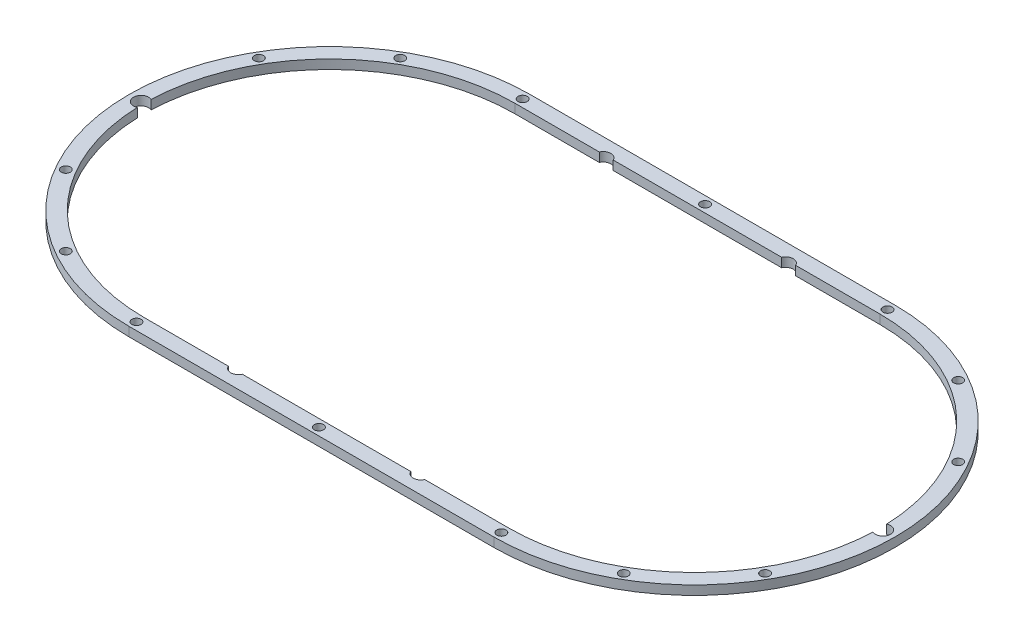
SolidWorks part; units mm, degrees
ref_plane "前视基准面" through (0, 0, 0) normal (0, 0, 1) x (1, 0, 0)
ref_plane "上视基准面" through (0, 0, 0) normal (0, 1, 0) x (1, 0, 0)
ref_plane "右视基准面" through (0, 0, 0) normal (1, 0, 0) x (0, 0, -1)
sketch "草图1" plane through (0, 0, 0) normal (0, 1, 0) x (1, 0, 0)
  line L0 (0, 0) -> (0, 89.0672) construction
  line L1 (-60, 0) -> (60, 0) construction
  line L2 (-60, 70) -> (60, 70)
  line L3 (-60, -70) -> (60, -70)
  line L4 (-90, 51.9615) -> (-60, 0) construction
  line L5 (-90, -51.9615) -> (-60, 0) construction
  line L8 (0, 0) -> (76.6344, 0) construction
  line L9 (-49.5811, 59.0885) -> (-60, 0) construction
  line L10 (-116.3816, -20.5212) -> (-60, 0) construction
  line L11 (-14.0373, -38.5673) -> (-60, 0) construction
  arc A2 (-60, 70) -> (-60, -70) centre (-60, 0) ccw
  arc A3 (60, -70) -> (60, 70) centre (60, 0) ccw
  circle A4 centre (0, 0) radius 1.5 construction
  circle A5 centre (-90, 51.9615) radius 1.5 construction
  circle A6 centre (-90, -51.9615) radius 1.5 construction
  circle A7 centre (90, -51.9615) radius 1.5 construction
  circle A8 centre (90, 51.9615) radius 1.5 construction
  circle A10 centre (-122, 0) radius 1.5
  circle A11 centre (122, 0) radius 1.5
  circle A12 centre (-30, 60) radius 1.5
  circle A13 centre (30, 60) radius 1.5
  circle A14 centre (30, -60) radius 1.5
  circle A15 centre (-30, -60) radius 1.5
  point P1 (0, 0)
  point P7 (0, 0)
  dimension "D4" = 3
  dimension "D7" = 3
  dimension "D9" = 3
  dimension "D10" = 60
  dimension "D12" = 3
  dimension "D13" = 62
  dimension "D14" = 62
  dimension "D15" = 3
  dimension "D16" = 3
  dimension "D18" = 60
  dimension "D8" = 120
  dimension "D11" = 120
  dimension "D17" = 30
  dimension "D20" = 60
  dimension "D21" = 80
  dimension "D24" = 120
  dimension "D26" = 60
  dimension "D27" = 120
extrude "凸台-拉伸2" add sketch "草图1" along normal blind 3
sketch "草图3" plane through (0, 3, 0) normal (0, 1, 0) x (1, 0, 0)
  line L2 (-60, -66) -> (60, -66)
  line L3 (60, 66) -> (-60, 66)
  line L4 (-60, -70) -> (60, -70)
  line L5 (60, 70) -> (-60, 70)
  line L6 (-60, -70) -> (60, -70)
  line L7 (60, 70) -> (-60, 70)
  arc A2 (60, -66) -> (60, 66) centre (60, 0) ccw
  arc A3 (-60, 66) -> (-60, -66) centre (-60, 0) ccw
  arc A4 (60, -70) -> (60, 70) centre (60, 0) ccw
  arc A5 (-60, 70) -> (-60, -70) centre (-60, 0) ccw
  arc A6 (60, -70) -> (60, 70) centre (60, 0) ccw
  arc A7 (-60, 70) -> (-60, -70) centre (-60, 0) ccw
  dimension "D1" = 0
  dimension "D2" = 4
extrude "切除-拉伸1" cut sketch "草图3" against normal blind 10
sketch "草图4" plane through (0, 3, 0) normal (0, 1, 0) x (1, 0, 0)
  line L0 (60, 36) -> (-60, 36) construction
  line L1 (-60, -36) -> (60, -36) construction
  line L2 (60, 66) -> (-60, 66)
  line L3 (-60, -66) -> (60, -66)
  line L4 (60, 66) -> (-60, 66) construction
  line L5 (-60, -66) -> (60, -66) construction
  line L6 (-85.4558, -25.4558) -> (-60, 0) construction
  line L7 (-60, 0) -> (-39.3991, 0) construction
  line L8 (0, 0) -> (-22.7346, 0) construction
  line L9 (0, 0) -> (0, 17.2758) construction
  arc A0 (-60, 36) -> (-60, -36) centre (-60, 0) ccw construction
  arc A1 (60, -36) -> (60, 36) centre (60, 0) ccw construction
  arc A2 (-60, 66) -> (-60, -66) centre (-60, 0) ccw
  arc A3 (60, -66) -> (60, 66) centre (60, 0) ccw
  arc A4 (-60, 66) -> (-60, -66) centre (-60, 0) ccw construction
  arc A5 (60, -66) -> (60, 66) centre (60, 0) ccw construction
  circle A6 centre (-96, 0) radius 7.5
  circle A7 centre (96, 0) radius 7.5
  circle A8 centre (0, 36) radius 7.5
  circle A9 centre (0, -36) radius 7.5
  circle A10 centre (-60, -36) radius 7.5
  circle A11 centre (60, -36) radius 7.5
  circle A12 centre (30, -36) radius 7.5
  circle A13 centre (-30, -36) radius 7.5
  circle A14 centre (-85.4558, -25.4558) radius 7.5
  circle A15 centre (60, 36) radius 7.5
  circle A16 centre (30, 36) radius 7.5
  circle A17 centre (-85.4558, 25.4558) radius 7.5
  circle A18 centre (-30, 36) radius 7.5
  circle A19 centre (-60, 36) radius 7.5
  circle A20 centre (85.4558, -25.4558) radius 7.5
  circle A21 centre (85.4558, 25.4558) radius 7.5
  dimension "D3" = 15
  dimension "D4" = 15
  dimension "D5" = 15
  dimension "D6" = 15
  dimension "D7" = 15
  dimension "D8" = 15
  dimension "D10" = 15
  dimension "D11" = 30
  dimension "D12" = 15
  dimension "D2" = 30
  dimension "D9" = 2
  dimension "D13" = 135
  dimension "D1" = 0
extrude "切除-拉伸2" cut sketch "草图4" against normal blind 10
sketch "草图5" plane through (0, 3, 0) normal (0, 1, 0) x (1, 0, 0)
  line L0 (60, 61) -> (32.2913, 61) construction
  line L1 (-60, -61) -> (-32.2913, -61) construction
  line L2 (60, 66) -> (-60, 66)
  line L3 (-60, -66) -> (60, -66)
  line L4 (60, 66) -> (-60, 66) construction
  line L5 (-60, -66) -> (60, -66) construction
  line L6 (-32.2913, 61) -> (-60, 61) construction
  line L7 (60, 61) -> (-60, 61) construction
  line L8 (27.7087, 61) -> (-27.7087, 61) construction
  line L9 (-27.7087, -61) -> (27.7087, -61) construction
  line L10 (-60, -61) -> (60, -61) construction
  line L11 (32.2913, -61) -> (60, -61) construction
  line L12 (0, 0) -> (30, 0) construction
  line L13 (0, 0) -> (0, 14.6541) construction
  line L14 (114.9926, 31.75) -> (60, 0) construction
  line L15 (91.75, 54.9926) -> (60, 0) construction
  arc A0 (-60, 61) -> (-120.9577, 2.2723) centre (-60, 0) ccw construction
  arc A1 (60, -61) -> (120.9577, -2.2723) centre (60, 0) ccw construction
  arc A2 (-60, 66) -> (-60, -66) centre (-60, 0) ccw
  arc A3 (60, -66) -> (60, 66) centre (60, 0) ccw
  arc A4 (-60, 66) -> (-60, -66) centre (-60, 0) ccw construction
  arc A5 (60, -66) -> (60, 66) centre (60, 0) ccw construction
  circle A6 centre (-60, 63.5) radius 1.5
  circle A7 centre (114.9926, 31.75) radius 1.5
  arc A8 (-27.7087, 61) -> (-32.2913, 61) centre (-30, 60) ccw construction
  arc A9 (32.2913, 61) -> (27.7087, 61) centre (30, 60) ccw construction
  arc A10 (-120.9577, 2.2723) -> (-120.9577, -2.2723) centre (-122, 0) ccw construction
  arc A11 (-120.9577, -2.2723) -> (-60, -61) centre (-60, 0) ccw construction
  arc A12 (-60, 61) -> (-60, -61) centre (-60, 0) ccw construction
  arc A13 (120.9577, -2.2723) -> (120.9577, 2.2723) centre (122, 0) ccw construction
  arc A14 (120.9577, 2.2723) -> (60, 61) centre (60, 0) ccw construction
  arc A15 (60, -61) -> (60, 61) centre (60, 0) ccw construction
  arc A16 (-32.2913, -61) -> (-27.7087, -61) centre (-30, -60) ccw construction
  arc A17 (27.7087, -61) -> (32.2913, -61) centre (30, -60) ccw construction
  circle A19 centre (0, 63.5) radius 1.5
  circle A21 centre (60, 63.5) radius 1.5
  circle A22 centre (-30, 63.5) radius 1.5 [skipped]
  circle A23 centre (30, 63.5) radius 1.5 [skipped]
  circle A24 centre (60, 0) radius 63.5 construction
  circle A25 centre (91.75, 54.9926) radius 1.5
  circle A26 centre (91.75, -54.9926) radius 1.5
  circle A27 centre (114.9926, -31.75) radius 1.5
  circle A28 centre (-91.75, -54.9926) radius 1.5
  circle A29 centre (-114.9926, -31.75) radius 1.5
  circle A30 centre (-91.75, 54.9926) radius 1.5
  circle A31 centre (-114.9926, 31.75) radius 1.5
  circle A32 centre (60, -63.5) radius 1.5
  circle A33 centre (0, -63.5) radius 1.5
  circle A34 centre (-60, -63.5) radius 1.5
  point P59 (0, 0)
  dimension "D3" = 3
  dimension "D4" = 2.5
  dimension "D5" = 5
  dimension "D6" = 5
  dimension "D7" = 5
  dimension "D8" = 5
  dimension "D9" = 5
  dimension "D10" = 5
  dimension "D12" = 3
  dimension "D13" = 2.5
  dimension "D15" = 3
  dimension "D14" = 30
  dimension "D16" = 30
  dimension "D1" = 0
  dimension "D2" = 5
  dimension "D11" = 5
extrude "切除-拉伸3" cut sketch "草图5" against normal blind 10
sketch "草图6" plane through (0, 3, 0) normal (0, 1, 0) x (1, 0, 0)
  line L0 (60, 61) -> (32.2913, 61)
  line L1 (-60, -61) -> (-32.2913, -61)
  line L6 (-32.2913, 61) -> (-60, 61)
  line L7 (-27.7087, -61) -> (27.7087, -61)
  line L8 (32.2913, -61) -> (60, -61)
  line L9 (27.7087, 61) -> (-27.7087, 61)
  arc A0 (-60, 61) -> (-120.9577, 2.2723) centre (-60, 0) ccw
  arc A1 (60, -61) -> (120.9577, -2.2723) centre (60, 0) ccw
  arc A6 (-27.7087, 61) -> (-32.2913, 61) centre (-30, 60) ccw construction
  arc A7 (-27.7087, 61) -> (-32.2913, 61) centre (-30, 60) ccw
  arc A8 (-32.2913, -61) -> (-27.7087, -61) centre (-30, -60) ccw construction
  arc A9 (27.7087, -61) -> (32.2913, -61) centre (30, -60) ccw construction
  arc A10 (32.2913, 61) -> (27.7087, 61) centre (30, 60) ccw construction
  arc A11 (-32.2913, -61) -> (-27.7087, -61) centre (-30, -60) ccw
  arc A12 (27.7087, -61) -> (32.2913, -61) centre (30, -60) ccw
  arc A13 (32.2913, 61) -> (27.7087, 61) centre (30, 60) ccw
  arc A14 (120.9577, -2.2723) -> (120.9577, 2.2723) centre (122, 0) ccw construction
  arc A15 (-120.9577, 2.2723) -> (-120.9577, -2.2723) centre (-122, 0) ccw construction
  arc A16 (120.9577, -2.2723) -> (120.9577, 2.2723) centre (122, 0) ccw
  arc A17 (-120.9577, 2.2723) -> (-120.9577, -2.2723) centre (-122, 0) ccw
  arc A18 (120.9577, 2.2723) -> (60, 61) centre (60, 0) ccw
  arc A19 (-120.9577, -2.2723) -> (-60, -61) centre (-60, 0) ccw
extrude "切除-拉伸4" cut sketch "草图6" against normal blind 10
